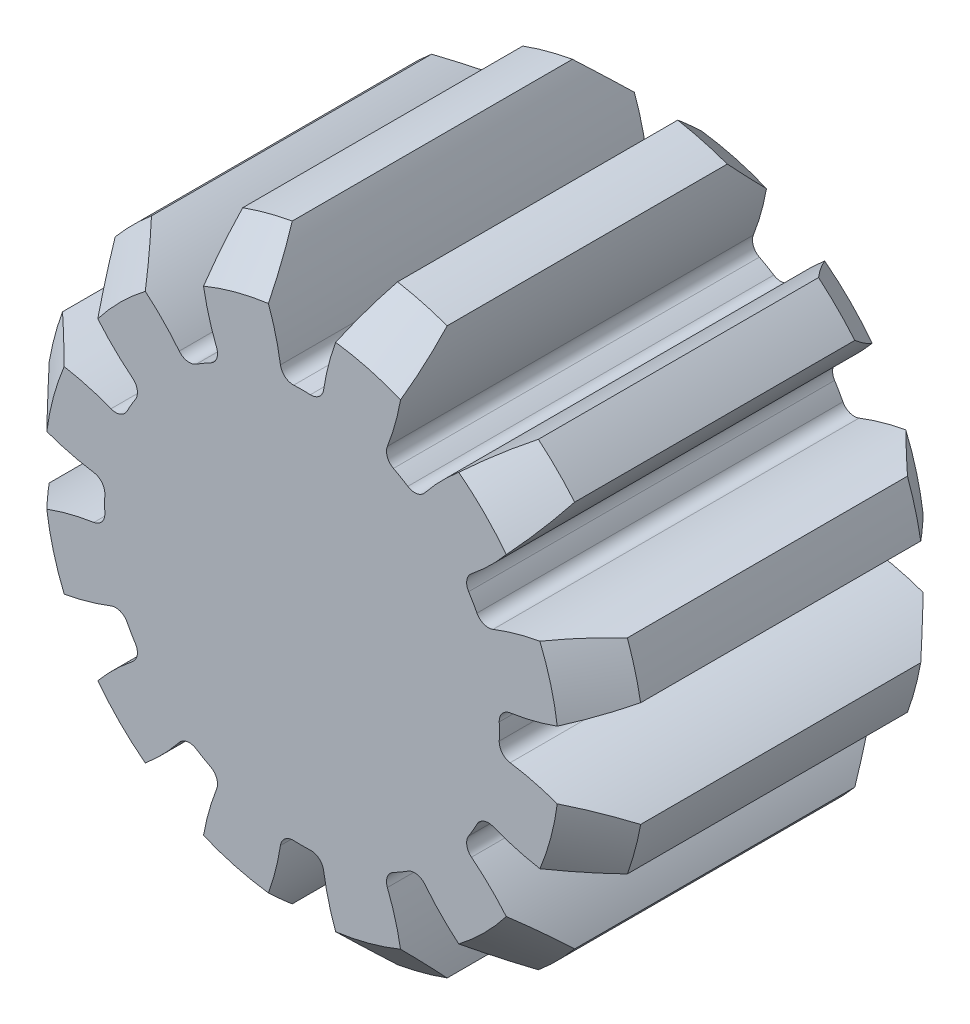
SolidWorks part; units mm, degrees
ref_plane "Front Plane" through (0, 0, 0) normal (0, 0, 1) x (1, 0, 0)
ref_plane "Top Plane" through (0, 0, 0) normal (0, 1, 0) x (1, 0, 0)
ref_plane "Right Plane" through (0, 0, 0) normal (1, 0, 0) x (0, 0, -1)
sketch "Sketch1" plane through (0, 0, 0) normal (0, 0, 1) x (1, 0, 0)
  circle A1 centre (0, 0) radius 3.7286 construction
  circle A2 centre (0, 0) radius 4.35
  dimension "D1" = 7.4571
  dimension "D2" = 8.7
extrude "Boss-Extrude1" add sketch "Sketch1" along normal mid plane 5.3
sketch "Sketch2" plane through (0, 0, 0) normal (0, 0, 1) x (1, 0, 0)
  line L0 (0, 4.35) -> (0, 0) construction
  line L1 (0, 0) -> (2.175, 3.7672) construction
  line L2 (0, 0) -> (1.1259, 4.2018) construction
  line L3 (-0.291, 2.8437) -> (0, 0) construction
  line L4 (-0.4867, 3.6967) -> (0.4867, 3.6967) construction
  line L5 (0.4867, 3.6967) -> (1.4269, 3.4448) construction
  line L6 (-0.7036, 4.2927) -> (0, 2.3595) construction
  circle A0 centre (0, 0) radius 3.1071 construction
  arc A1 (0.291, 2.8437) -> (-0.291, 2.8437) centre (0, 0) ccw
  circle A2 centre (0, 0) radius 4.35 construction
  arc A3 (-0.7628, 4.2826) -> (-0.291, 2.8437) centre (-3.8232, 2.4823) cw
  circle A4 centre (0, 0) radius 4.35 construction
  arc A5 (0.7628, 4.2826) -> (0.291, 2.8437) centre (3.8232, 2.4823) ccw
  circle A6 centre (0, 0) radius 3.7286 construction
  arc A7 (0.7628, 4.2826) -> (-0.7628, 4.2826) centre (0, 0) ccw
  point P3 (0, 0)
  point P24 (0, 2.3595)
  point P25 (0, 2.3595)
  point P26 (0, 2.3176)
  dimension "D1" = 30
  dimension "D2" = 1.2429
  dimension "D3" = 1.4914
  dimension "D4" = 20
extrude "Cut-Extrude1" cut sketch "Sketch2" against normal through all both and the other way through all
fillet "Fillet1" radius 0.1864 2 edges at (0.291, 2.8437, 0) (-0.291, 2.8437, 0)
chamfer "Chamfer1" distance 0.6214 angle 45 2 edges at (0, -4.35, -2.65) (0, -4.35, 2.65)
pattern_circular "CirPattern1" count 12 over 360 about axis through (0, 0, 0) along (0, 0, 1) of "Cut-Extrude1", "Fillet1"
equation "\"Module\" = 0.6214285714285714285714"
equation "\"Number of Teeth\"= 12"
equation "\"Pressure Angle\" = 20'."
equation "\"D1@Sketch1\"=\"Module\"*\"Number of Teeth\""
equation "\"D2@Sketch1\"=(\"Number of Teeth\" + 2) *\"Module\""
equation "\"D1@Sketch2\"=360 / \"Number of Teeth\""
equation "\"D2@Sketch2\"= \"Module\" * 2"
equation "\"D3@Sketch2\"=\"Module\"*if(\"Module\" => 1.25, 2.25,2.4)"
equation "\"D4@Sketch2\"=\"Pressure Angle\""
equation "\"D1@Fillet1\"=\"Module\"*0.3"
equation "\"D1@CirPattern1\"=\"Number of Teeth\""
equation "\"D1@Chamfer1\"=\"Module\""
